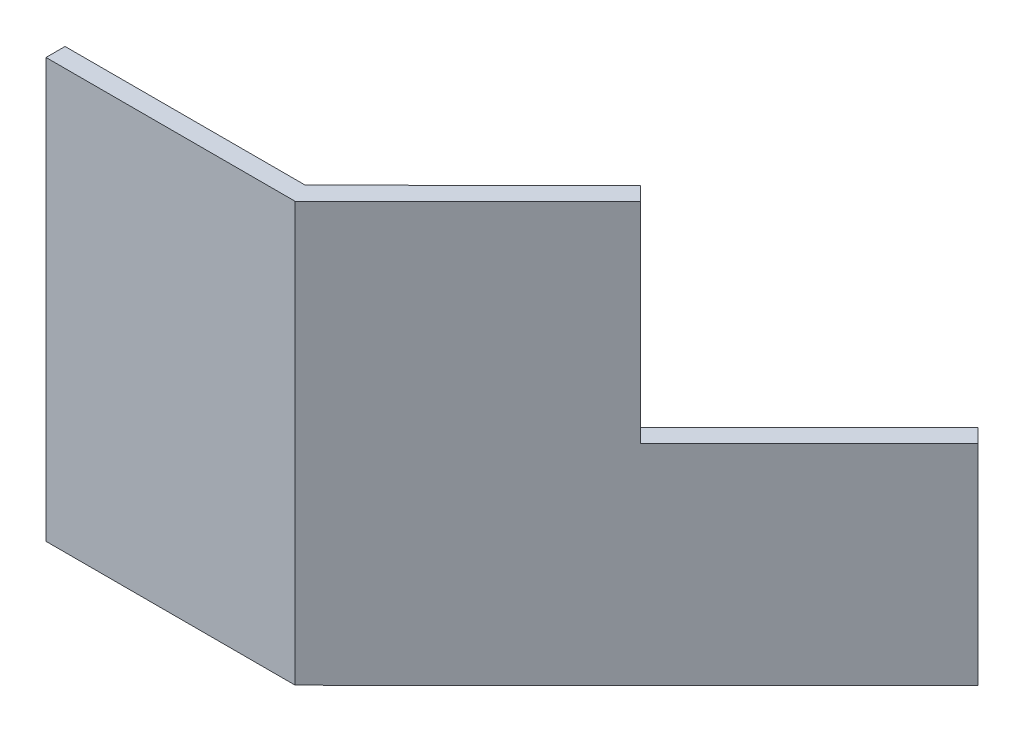
SolidWorks part; units mm, degrees
ref_plane "Front Plane" through (0, 0, 0) normal (0, 0, 1) x (1, 0, 0)
ref_plane "Top Plane" through (0, 0, 0) normal (0, 1, 0) x (1, 0, 0)
ref_plane "Right Plane" through (0, 0, 0) normal (1, 0, 0) x (0, 0, -1)
sketch "Sketch1" plane through (0, 0, 0) normal (0, 1, 0) x (1, 0, 0)
  line L1 (-0.2536, 0) -> (-4.6234, 0)
  line L3 (-0.0925, -0.3464) -> (-4.6234, -0.3464)
  line L4 (-4.6234, 0) -> (-4.6234, -0.3464)
  line L5 (-0.0925, -0.3464) -> (6.1198, 5.8559)
  line L6 (-0.2536, 0) -> (5.8662, 6.1099)
  line L7 (6.1198, 5.8559) -> (5.8662, 6.1099)
  line L8 (14.3962, 14.6261) -> (14.6497, 14.3721)
extrude "Boss-Extrude1" add sketch "Sketch1" along normal blind 7.62 contours L1 L4 L3 L5 L7 L6
sketch "Sketch3" plane through (0, 7.62, 0) normal (0, 1, 0) x (1, 0, 0)
  line L0 (6.1198, 5.8559) -> (5.8662, 6.1099)
  line L1 (6.1198, 5.8559) -> (3.0474, 2.7884)
  line L2 (5.8662, 6.1099) -> (2.7938, 3.0424)
  line L3 (3.0474, 2.7884) -> (2.7938, 3.0424)
extrude "Cut-Extrude2" cut sketch "Sketch3" against normal blind 3.81
ref_plane "Plane1" through (-0.2536, 7.62, 0) normal (-1, 0, 0) x (0, 0, 1)
sketch "Sketch5" plane through (0, 7.62, 0) normal (0, 1, 0) x (1, 0, 0)
  line L1 (-0.0925, -0.3464) -> (-4.6234, -0.3464) construction
  line L2 (-2.358, -0.3464) -> (-2.358, 0)
  line L3 (-0.2536, 0) -> (-4.6234, 0) construction
